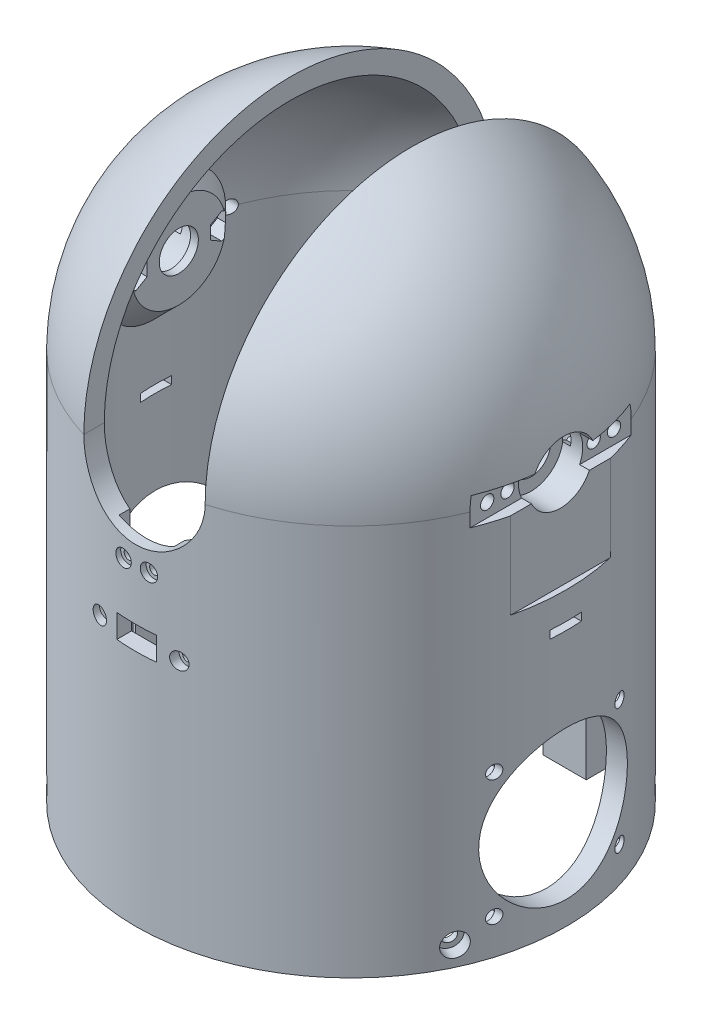
SolidWorks part; units mm, degrees
material "PLA"
ref_plane "Alzado" through (0, 0, 0) normal (0, 0, 1) x (1, 0, 0)
ref_plane "Planta" through (0, 0, 0) normal (0, 1, 0) x (1, 0, 0)
ref_plane "Vista lateral" through (0, 0, 0) normal (1, 0, 0) x (0, 0, -1)
sketch "Croquis1" plane through (0, 0, 0) normal (0, 0, 1) x (1, 0, 0)
  line L0 (0, 176.4295) -> (0, -176.4295) construction
  line L2 (50, 100) -> (50, 0)
  line L3 (50, 0) -> (55, 0)
  line L4 (55, 100) -> (55, 0)
  line L5 (0, 155) -> (0, 150)
  arc A1 (50, 100) -> (0, 150) centre (0, 100) ccw
  arc A2 (55, 100) -> (0, 155) centre (0, 100) ccw
  dimension "D1" = 55
  dimension "D2" = 5
  dimension "D3" = 100
revolve "Revolución1" add sketch "Croquis1" angle 360 about L0
sketch "Croquis2" plane through (0, 0, 0) normal (0, 0, 1) x (1, 0, 0)
  line L2 (15.5, 100) -> (15.5, 160)
  line L3 (15.5, 160) -> (-15.5, 160)
  line L4 (-15.5, 100) -> (-15.5, 160)
  arc A0 (-15.5, 100) -> (15.5, 100) centre (0, 100) ccw
  point P2 (0, 115.5)
  dimension "D3" = 15.5
  dimension "D1" = 60
  dimension "D2" = 100
extrude "Cortar-Extruir1" cut sketch "Croquis2" against normal blind 95 and the other way blind 84
sketch "Croquis3" plane through (0, 0, 0) normal (0, 0, 1) x (1, 0, 0)
  line L0 (-50, 118) -> (-50, 100)
  line L1 (-50, 100) -> (-44, 100)
  line L2 (-44, 100) -> (-44, 112)
  line L3 (-44, 112) -> (-50, 118)
  line L4 (-69.5096, 100) -> (-28.9792, 100) construction
  line L5 (-55, 100) -> (-15.5, 100) construction
  dimension "D1" = 6
  dimension "D2" = 18
  dimension "D3" = 12
  dimension "D4" = 50
  dimension "D5" = 100
revolve "Revolución2" add sketch "Croquis3" angle 360 about L4
sketch "Croquis4" plane through (-44, 0, 0) normal (1, 0, 0) x (0, 0, -1)
  circle A0 centre (0, 100) radius 5
  dimension "D1" = 10
extrude "Cortar-Extruir2" cut sketch "Croquis4" against normal blind 26
ref_plane "Plano1" through (-55, 0, 0) normal (-1, 0, 0) x (0, 0, 1)
sketch "Croquis5" plane through (-55, 0, 0) normal (-1, 0, 0) x (0, 0, 1)
  circle A0 centre (0, 100) radius 8.2
  dimension "D1" = 16.4
extrude "Cortar-Extruir3" cut sketch "Croquis5" against normal blind 9
sketch "Croquis6" plane through (-55, 0, 0) normal (-1, 0, 0) x (0, 0, 1)
  line L1 (25, 96.5) -> (-25, 96.5)
  line L2 (25, 96.5) -> (25, 103.5)
  line L3 (25, 103.5) -> (-25, 103.5)
  line L4 (-25, 96.5) -> (-25, 103.5)
  line L5 (25, 96.5) -> (-25, 103.5) construction
  line L6 (25, 103.5) -> (-25, 96.5) construction
  point P0 (0, 100)
  dimension "D1" = 7
  dimension "D2" = 50
extrude "Cortar-Extruir4" cut sketch "Croquis6" against normal blind 4
sketch "Croquis7" plane through (-51, 0, 0) normal (-1, 0, 0) x (0, 0, 1)
  line L0 (-11, 100) -> (11, 100) construction
  line L1 (11, 100) -> (16.2, 100) construction
  line L2 (0, 100) -> (0, 107.1704) construction
  circle A0 centre (-11, 100) radius 1.7
  circle A1 centre (11, 100) radius 1.7
  circle A2 centre (16.2, 100) radius 1.7
  circle A3 centre (0, 100) radius 5 construction
  circle A4 centre (-16.2, 100) radius 1.7
  point P4 (0, 100)
  dimension "D2" = 3.4
  dimension "D1" = 22
  dimension "D3" = 5.2
extrude "Cortar-Extruir5" cut sketch "Croquis7" against normal blind 10
sketch "Croquis8" plane through (-44, 0, 0) normal (1, 0, 0) x (0, 0, -1)
  line L1 (-11, 96.65) -> (-8.0988, 98.325)
  line L2 (-8.0988, 98.325) -> (-8.0988, 101.675)
  line L3 (-8.0988, 101.675) -> (-11, 103.35)
  line L4 (-11, 103.35) -> (-13.9012, 101.675)
  line L5 (-13.9012, 101.675) -> (-13.9012, 98.325)
  line L6 (-13.9012, 98.325) -> (-11, 96.65)
  line L7 (11, 96.65) -> (13.9012, 98.325)
  line L8 (13.9012, 98.325) -> (13.9012, 101.675)
  line L9 (13.9012, 101.675) -> (11, 103.35)
  line L10 (11, 103.35) -> (8.0988, 101.675)
  line L11 (8.0988, 101.675) -> (8.0988, 98.325)
  line L12 (8.0988, 98.325) -> (11, 96.65)
  circle A0 centre (-11, 100) radius 3.35 construction
  circle A1 centre (11, 100) radius 3.35 construction
  dimension "D1" = 6.7
extrude "Cortar-Extruir6" cut sketch "Croquis8" against normal blind 4
mirror "Simetría1" about plane through (0, 0, 0) normal (1, 0, 0) of "Cortar-Extruir2", "Revolución2", "Cortar-Extruir6", "Cortar-Extruir4", "Cortar-Extruir5", "Cortar-Extruir3"
sketch "Croquis9" plane through (0, 0, 0) normal (0, -1, 0) x (1, 0, 0)
  line L1 (-38.9, -27) -> (-27.9, -27)
  line L2 (-38.9, -27) -> (-38.9, -31.4132)
  line L4 (-27.9, -27) -> (-27.9, -41.492)
  line L7 (14.1, -35) -> (25.1, -35)
  line L8 (14.1, -35) -> (14.1, -47.9707)
  line L10 (25.1, -35) -> (25.1, -43.2434)
  arc A0 (-38.9, -31.4132) -> (-27.9, -41.492) centre (0, 0) ccw
  arc A2 (14.1, -47.9707) -> (25.1, -43.2434) centre (0, 0) ccw
  arc A3 (-47.5278, -15.5278) -> (15.5, 47.5368) centre (0, 0) ccw construction
  dimension "D1" = 11
  dimension "D2" = 27
  dimension "D3" = 27.9
  dimension "D4" = 35
  dimension "D5" = 14.1
  dimension "D6" = 11
extrude "Saliente-Extruir1" add sketch "Croquis9" against normal blind 55
sketch "Croquis10" plane through (0, 0, 0) normal (0, -1, 0) x (1, 0, 0)
  line L0 (-27.9, -41.492) -> (-21.0565, -41.492)
  line L1 (-21.0565, -41.492) -> (-21.0565, -45.35)
  line L2 (-21.0565, -45.35) -> (-24.1, -45.35)
  line L3 (-24.1, -45.35) -> (-27.9, -43)
  line L4 (-27.9, -43) -> (-27.9, -41.492)
  line L5 (-32, -29.5) -> (-32, -39.5)
  line L6 (-32, -39.5) -> (-26.0412, -34.5)
  line L7 (-26.0412, -34.5) -> (-32, -29.5)
  line L8 (-27.9, -27) -> (-38.9, -27) construction
  line L9 (18.2, -37.5) -> (18.2, -47.5)
  line L10 (18.2, -47.5) -> (12.2412, -42.5)
  line L11 (12.2412, -42.5) -> (18.2, -37.5)
  line L12 (25.1, -35) -> (14.1, -35) construction
  line L13 (14.1, -35) -> (14.1, -47.9707) construction
  arc A0 (-47.5278, -15.5278) -> (15.5, 47.5368) centre (0, 0) ccw construction
  arc A1 (-27.9, -41.492) -> (14.1, -47.9707) centre (0, 0) ccw construction
  dimension "D1" = 3.8
  dimension "D2" = 2.35
  dimension "D3" = 10
  dimension "D4" = 4.1
  dimension "D5" = 50
  dimension "D6" = 50
  dimension "D7" = 7.5
  dimension "D8" = 8.5
  dimension "D9" = 7.5
  dimension "D10" = 4.1
  dimension "D11" = 50
  dimension "D12" = 50
  dimension "D13" = 10
extrude "Cortar-Extruir7" cut sketch "Croquis10" against normal up to surface (55 mm away) up to face at (19.6355, 55, -40.3861)
pattern_circular "MatrizC1" count 2 over 360 about axis through (0, 0, 0) along (0, 1, 0) of "Cortar-Extruir7", "Saliente-Extruir1"
ref_plane "Plano2" through (-38.8909, 0, 38.8909) normal (-0.7071, 0, 0.7071) x (0, 1, 0)
sketch "Croquis11" plane through (-38.8909, 0, 38.8909) normal (-0.7071, 0, 0.7071) x (0, 1, 0)
  circle A0 centre (5, 0) radius 1.7
  dimension "D2" = 3.4
  dimension "D1" = 5
extrude "Cortar-Extruir8" cut sketch "Croquis11" against normal blind 10
sketch "Croquis12" plane through (-38.8909, 0, 38.8909) normal (-0.7071, 0, 0.7071) x (0, 1, 0)
  circle A0 centre (5, 0) radius 2.95
  dimension "D1" = 5.9
extrude "Cortar-Extruir9" cut sketch "Croquis12" against normal blind 3.35
pattern_circular "MatrizC2" count 2 over 290 about axis through (0, 0, 0) along (0, 1, 0) of "Cortar-Extruir8", "Cortar-Extruir9"
pattern_circular "MatrizC3" count 2 over 360 about axis through (0, 0, 0) along (0, 1, 0) of "MatrizC2", "Cortar-Extruir8", "Cortar-Extruir9"
sketch "Croquis13" plane through (0, 0, 0) normal (0, 0, 1) x (1, 0, 0)
  line L0 (-55, 0) -> (55, 0) construction
  line L1 (-7, 102) -> (7, 102)
  line L2 (-7, 102) -> (-7, 72)
  line L3 (-7, 72) -> (7, 72)
  line L4 (7, 102) -> (7, 72)
  line L5 (-7, 102) -> (7, 72) construction
  line L6 (-7, 72) -> (7, 102) construction
  point P0 (0, 87)
  dimension "D1" = 14
  dimension "D2" = 30
  dimension "D3" = 72
extrude "Cortar-Extruir10" cut sketch "Croquis13" along normal blind 52.25
sketch "Croquis14" plane through (0, 0, 52.25) normal (0, 0, -1) x (-1, 0, 0)
  line L0 (-3.25, 79.9) -> (3.25, 79.9) construction
  line L4 (0, 72) -> (0, 87.8) construction
  line L5 (7, 72) -> (-7, 72) construction
  line L6 (7, 72) -> (-7, 72) construction
  circle A2 centre (-3.25, 79.9) radius 1.2
  circle A3 centre (3.25, 79.9) radius 1.2
  point P2 (0, 79.9)
  dimension "D2" = 2.4
  dimension "D1" = 7.9
  dimension "D3" = 6.5
extrude "Cortar-Extruir11" cut sketch "Croquis14" against normal blind 7.25
ref_plane "Plano3" through (0, 0, 55) normal (0, 0, 1) x (1, 0, 0)
sketch "Croquis15" plane through (0, 0, 55) normal (0, 0, 1) x (1, 0, 0)
  circle A0 centre (-3.25, 79.9) radius 2.1
  circle A1 centre (3.25, 79.9) radius 2.1
  dimension "D1" = 4.2
extrude "Cortar-Extruir12" cut sketch "Croquis15" against normal blind 1.5
sketch "Croquis16" plane through (0, 0, 0) normal (0, 0, 1) x (1, 0, 0)
  line L1 (-13.5, 69.375) -> (13.5, 69.375)
  line L2 (-13.5, 69.375) -> (-13.5, 57.375)
  line L3 (-13.5, 57.375) -> (13.5, 57.375)
  line L4 (13.5, 69.375) -> (13.5, 57.375)
  line L5 (-13.5, 69.375) -> (13.5, 57.375) construction
  line L6 (-13.5, 57.375) -> (13.5, 69.375) construction
  point P0 (0, 63.375)
  dimension "D1" = 27
  dimension "D2" = 12
  dimension "D3" = 57.375
extrude "Cortar-Extruir13" cut sketch "Croquis16" along normal blind 51
sketch "Croquis17" plane through (0, 0, 51) normal (0, 0, -1) x (-1, 0, 0)
  line L0 (-10.16, 63.375) -> (10.16, 63.375) construction
  line L2 (0, 69.375) -> (0, 57.375) construction
  line L3 (-13.5, 69.375) -> (13.5, 69.375) construction
  line L4 (13.5, 57.375) -> (-13.5, 57.375) construction
  line L6 (5.075, 60.875) -> (-5.075, 60.875)
  line L7 (5.075, 60.875) -> (5.075, 66.875)
  line L8 (5.075, 66.875) -> (-5.075, 66.875)
  line L9 (-5.075, 60.875) -> (-5.075, 66.875)
  line L10 (5.075, 60.875) -> (-5.075, 66.875) construction
  line L11 (5.075, 66.875) -> (-5.075, 60.875) construction
  line L12 (13.5, 57.375) -> (-13.5, 57.375) construction
  circle A0 centre (-10.16, 63.375) radius 1.2
  circle A1 centre (10.16, 63.375) radius 1.2
  point P4 (0, 63.375)
  point P19 (0, 63.875)
  point P21 (0, 63.375)
  dimension "D6" = 2.4
  dimension "D1" = 20.32
  dimension "D2" = 3.5
  dimension "D3" = 6
  dimension "D4" = 10.15
  dimension "D5" = 6
extrude "Cortar-Extruir14" cut sketch "Croquis17" against normal blind 6
sketch "Croquis18" plane through (0, 0, 55) normal (0, 0, 1) x (1, 0, 0)
  circle A0 centre (-10.16, 63.375) radius 2.1
  circle A1 centre (10.16, 63.375) radius 2.1
  dimension "D1" = 4.2
extrude "Cortar-Extruir15" cut sketch "Croquis18" against normal blind 3
sketch "Croquis19" plane through (-55, 0, 0) normal (-1, 0, 0) x (0, 0, 1)
  line L1 (16, 9) -> (-16, 9) construction
  line L2 (16, 9) -> (16, 41) construction
  line L3 (16, 41) -> (-16, 41) construction
  line L4 (-16, 9) -> (-16, 41) construction
  line L5 (16, 9) -> (-16, 41) construction
  line L6 (16, 41) -> (-16, 9) construction
  circle A0 centre (-16, 41) radius 1.7
  circle A1 centre (16, 41) radius 1.7
  circle A2 centre (-16, 9) radius 1.7
  circle A3 centre (16, 9) radius 1.7
  circle A4 centre (0, 25) radius 19
  point P0 (0, 25)
  dimension "D1" = 32
  dimension "D2" = 38
  dimension "D4" = 3.4
  dimension "D3" = 25
extrude "Cortar-Extruir16" cut sketch "Croquis19" against normal blind 11
sketch "Croquis20" plane through (0, 0, 0) normal (1, 0, 0) x (0, 0, -1)
  line L0 (-35, 55) -> (-35, 0) construction
  line L1 (-16, 37.65) -> (-13.0988, 39.325)
  line L2 (-13.0988, 39.325) -> (-13.0988, 42.675)
  line L3 (-13.0988, 42.675) -> (-16, 44.35)
  line L4 (-16, 44.35) -> (-18.9012, 42.675)
  line L5 (-18.9012, 42.675) -> (-18.9012, 39.325)
  line L6 (-18.9012, 39.325) -> (-16, 37.65)
  line L7 (16, 37.65) -> (18.9012, 39.325)
  line L8 (18.9012, 39.325) -> (18.9012, 42.675)
  line L9 (18.9012, 42.675) -> (16, 44.35)
  line L10 (16, 44.35) -> (13.0988, 42.675)
  line L11 (13.0988, 42.675) -> (13.0988, 39.325)
  line L12 (13.0988, 39.325) -> (16, 37.65)
  line L13 (16, 5.65) -> (18.9012, 7.325)
  line L14 (18.9012, 7.325) -> (18.9012, 10.675)
  line L15 (18.9012, 10.675) -> (16, 12.35)
  line L16 (16, 12.35) -> (13.0988, 10.675)
  line L17 (13.0988, 10.675) -> (13.0988, 7.325)
  line L18 (13.0988, 7.325) -> (16, 5.65)
  line L19 (-16, 5.65) -> (-13.0988, 7.325)
  line L20 (-13.0988, 7.325) -> (-13.0988, 10.675)
  line L21 (-13.0988, 10.675) -> (-16, 12.35)
  line L22 (-16, 12.35) -> (-18.9012, 10.675)
  line L23 (-18.9012, 10.675) -> (-18.9012, 7.325)
  line L24 (-18.9012, 7.325) -> (-16, 5.65)
  circle A0 centre (-16, 41) radius 3.35 construction
  circle A1 centre (16, 41) radius 3.35 construction
  circle A2 centre (16, 9) radius 3.35 construction
  circle A3 centre (-16, 9) radius 3.35 construction
  dimension "D1" = 6.7
extrude "Cortar-Extruir17" cut sketch "Croquis20" against normal blind 51
mirror "Simetría2" about plane through (0, 0, 0) normal (1, 0, 0) of "Cortar-Extruir16", "Cortar-Extruir17"
sketch "Croquis21" plane through (-55, 0, 0) normal (-1, 0, 0) x (0, 0, 1)
  line L1 (-16.25, 96.5) -> (-3.5707, 96.5)
  line L2 (-16.25, 96.5) -> (-16.25, 74.5)
  line L3 (-16.25, 74.5) -> (16.25, 74.5)
  line L4 (16.25, 96.5) -> (16.25, 74.5)
  line L5 (-20.5913, 96.5) -> (-7.4155, 96.5) construction
  line L6 (3.5707, 96.5) -> (16.25, 96.5)
  circle A0 centre (0, 100) radius 5 construction
  arc A1 (-3.5707, 96.5) -> (3.5707, 96.5) centre (0, 100) ccw
  point P7 (0, 74.5)
  dimension "D1" = 32.5
  dimension "D2" = 25.5
extrude "Cortar-Extruir18" cut sketch "Croquis21" against normal blind 1.5
sketch "Croquis22" plane through (-55, 0, 0) normal (-1, 0, 0) x (0, 0, 1)
  line L0 (12.7574, 74.5) -> (-12.7574, 74.5) construction
  line L1 (-4, 67.5) -> (4, 67.5)
  line L2 (-4, 67.5) -> (-4, 65.5)
  line L3 (-4, 65.5) -> (4, 65.5)
  line L4 (4, 67.5) -> (4, 65.5)
  line L5 (-4, 67.5) -> (4, 65.5) construction
  line L6 (-4, 65.5) -> (4, 67.5) construction
  line L7 (12.7574, 74.5) -> (-12.7574, 74.5) construction
  point P0 (0, 66.5)
  point P5 (0, 0)
  point P8 (0, 74.5)
  dimension "D1" = 2
  dimension "D2" = 8
  dimension "D3" = 8
extrude "Cortar-Extruir19" cut sketch "Croquis22" against normal blind 10
mirror "Simetría3" about plane through (0, 0, 0) normal (1, 0, 0) of "Cortar-Extruir19", "Cortar-Extruir18"
